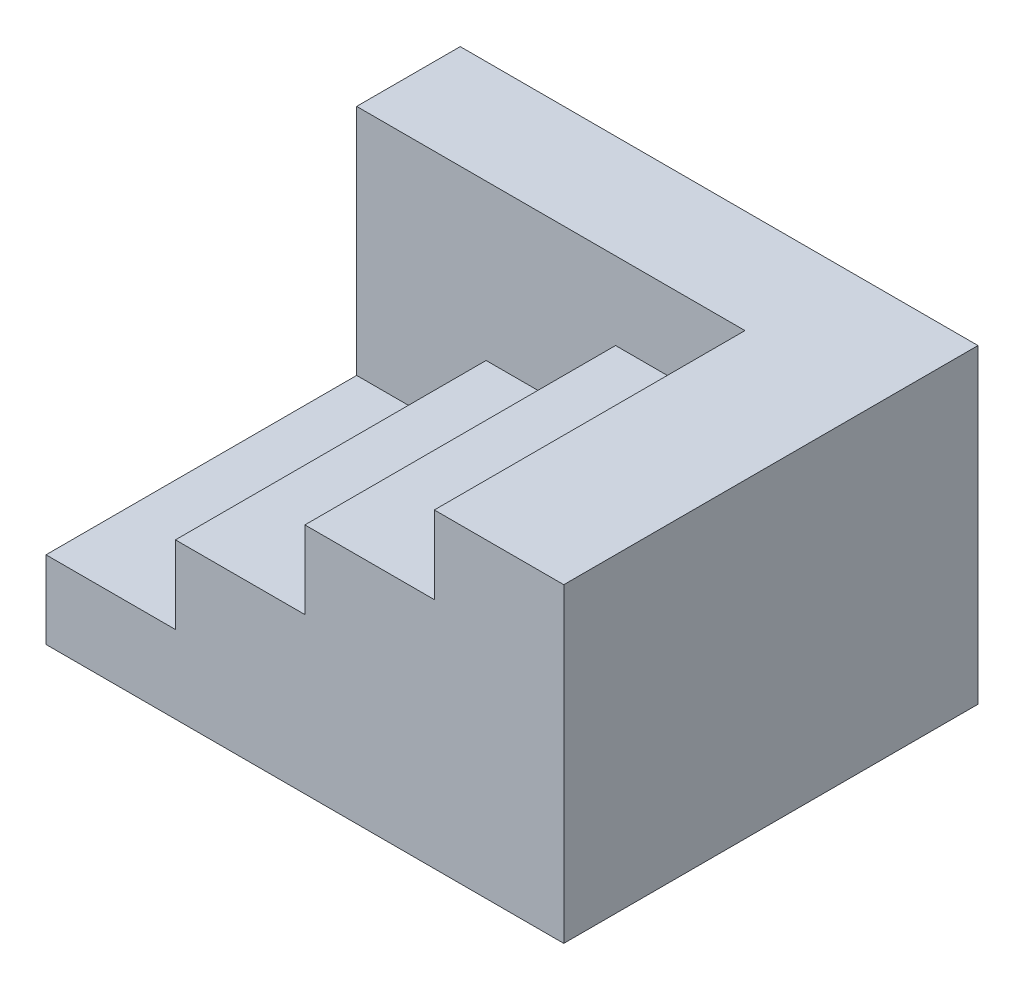
SolidWorks part; units mm, degrees
ref_plane "Front Plane" through (0, 0, 0) normal (0, 0, 1) x (1, 0, 0)
ref_plane "Top Plane" through (0, 0, 0) normal (0, 1, 0) x (1, 0, 0)
ref_plane "Right Plane" through (0, 0, 0) normal (1, 0, 0) x (0, 0, -1)
sketch "Sketch1" plane through (0, 0, 0) normal (0, 1, 0) x (1, 0, 0)
  line L1 (-50, 40) -> (50, 40)
  line L2 (-50, 40) -> (-50, -40)
  line L3 (-50, -40) -> (50, -40)
  line L4 (50, 40) -> (50, -40)
  dimension "D1" = 100
  dimension "D2" = 80
  dimension "D3" = 40
  dimension "D4" = 50
extrude "Boss-Extrude1" add sketch "Sketch1" along normal blind 60
sketch "Sketch2" plane through (0, 0, 40) normal (0, 0, 1) x (1, 0, 0)
  line L0 (-50, 60) -> (25, 60)
  line L1 (-50, 60) -> (50, 60) construction
  line L2 (25, 60) -> (25, 45)
  line L3 (25, 45) -> (0, 45)
  line L4 (0, 45) -> (0, 30)
  line L5 (0, 30) -> (-25, 30)
  line L6 (-25, 30) -> (-25, 15)
  line L7 (-25, 15) -> (-50, 15)
  line L8 (-50, 60) -> (-50, 0) construction
  line L9 (-50, 15) -> (-50, 60)
  dimension "D1" = 25
  dimension "D2" = 15
  dimension "D3" = 75
  dimension "D4" = 25
extrude "Cut-Extrude1" cut sketch "Sketch2" against normal blind 60
